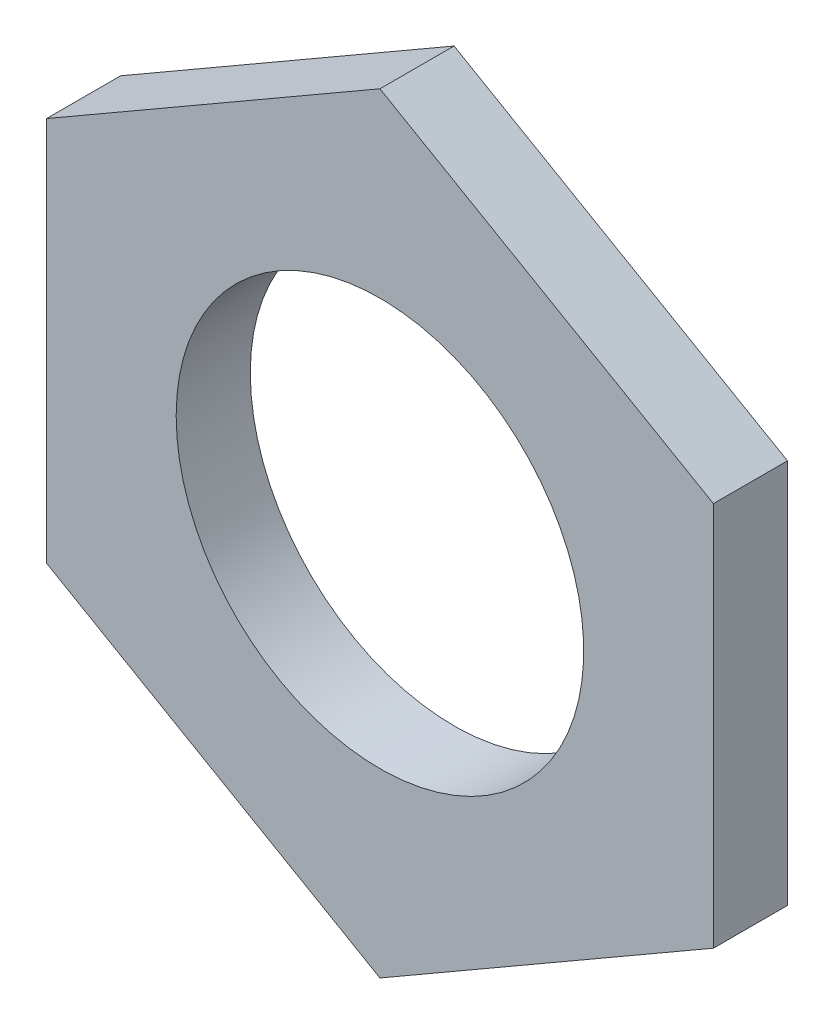
SolidWorks part; units mm, degrees
ref_plane "Plan de face" through (0, 0, 0) normal (0, 0, 1) x (1, 0, 0)
ref_plane "Plan de dessus" through (0, 0, 0) normal (0, 1, 0) x (1, 0, 0)
ref_plane "Plan de droite" through (0, 0, 0) normal (1, 0, 0) x (0, 0, -1)
sketch "Esquisse1" plane through (0, 0, 0) normal (0, 0, 1) x (1, 0, 0)
  line L1 (0, -15.5885) -> (13.5, -7.7942)
  line L2 (13.5, -7.7942) -> (13.5, 7.7942)
  line L3 (13.5, 7.7942) -> (0, 15.5885)
  line L4 (0, 15.5885) -> (-13.5, 7.7942)
  line L5 (-13.5, 7.7942) -> (-13.5, -7.7942)
  line L6 (-13.5, -7.7942) -> (0, -15.5885)
  circle A0 centre (0, 0) radius 13.5 construction
  dimension "D1" = 27
extrude "Boss.-Extru.1" add sketch "Esquisse1" along normal blind 3
hole_wizard "Trou pour taraudage pour trou taraudé M181" positions "Esquisse3" profile "Esquisse2" hole size "M18" standard "ISO" end condition through all
sketch "Esquisse3" plane through (0, 0, 0) normal (0, 0, -1) x (-1, 0, 0)
  point P3 (0, 0)
sketch "Esquisse2" plane through (0, 0, 0) normal (1, 0, 0) x (0, 1, 0)
  line L0 (0, 0) -> (0, 3)
  line L1 (0, 3) -> (8.25, 3)
  line L2 (8.25, 3) -> (8.25, 0)
  line L5 (8.25, 0) -> (0, 0)
  line L11 (0, -6.35) -> (0, 107.95) construction
  dimension "Diamètre du perçage jusqu'au prochain" = 16.5
  dimension "Profondeur du perçage jusqu'au prochain" = 3
